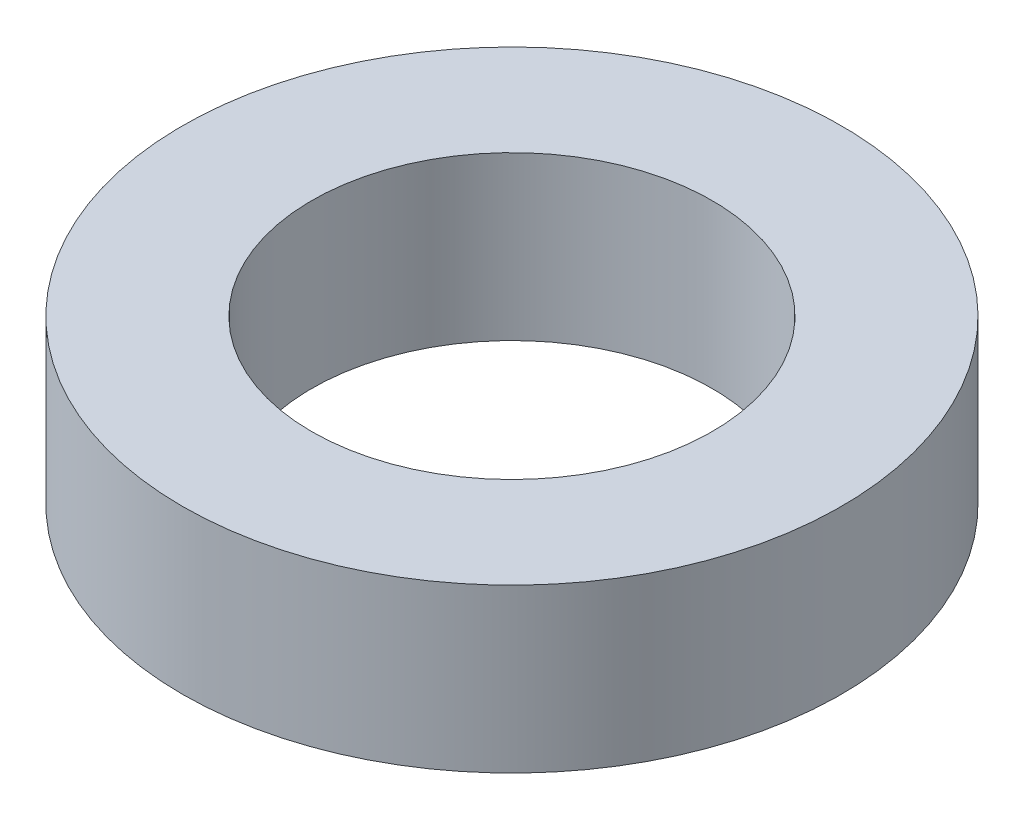
SolidWorks part; units mm, degrees
ref_plane "Спереди" through (0, 0, 0) normal (0, 0, 1) x (1, 0, 0)
ref_plane "Сверху" through (0, 0, 0) normal (0, 1, 0) x (1, 0, 0)
ref_plane "Справа" through (0, 0, 0) normal (1, 0, 0) x (0, 0, -1)
sketch "Эскиз1" plane through (0, 0, 0) normal (0, 1, 0) x (1, 0, 0)
  circle A0 centre (0, 0) radius 20.25
  circle A1 centre (0, 0) radius 12.3
  point P4 (-78.4219, 16.5364)
  dimension "D1" = 40.5
extrude "Бобышка-Вытянуть1" add sketch "Эскиз1" along normal blind 10
